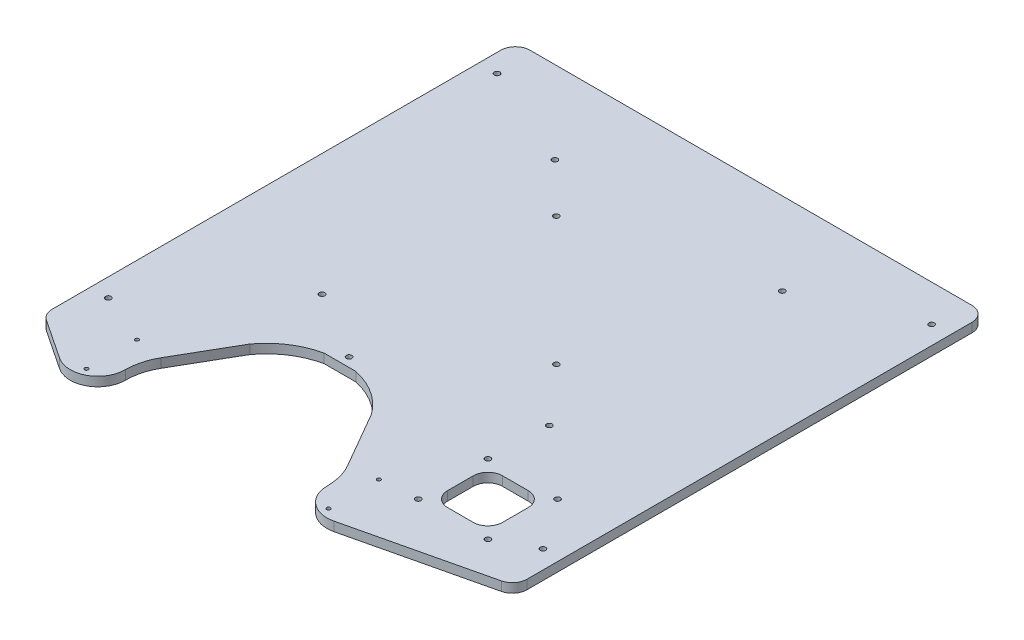
SolidWorks part; units mm, degrees
material "ABS PC"
ref_plane "Plan de face" through (0, 0, 0) normal (0, 0, 1) x (1, 0, 0)
ref_plane "Plan de dessus" through (0, 0, 0) normal (0, 1, 0) x (1, 0, 0)
ref_plane "Plan de droite" through (0, 0, 0) normal (1, 0, 0) x (0, 0, -1)
sketch "Esquisse1" plane through (0, 0, 0) normal (0, 1, 0) x (1, 0, 0)
  line L0 (-60.6815, -188.3301) -> (-75.8539, -214.6094) construction
  line L1 (-120.5, 31.2) -> (120.5, 31.2)
  line L2 (-128.5, 23.2) -> (-128.5, -221.5153)
  line L3 (-60.6815, -188.3301) -> (-75.8539, -214.6094)
  line L4 (128.5, 23.2) -> (128.5, -219.4674)
  line L5 (25.8539, -214.6094) -> (10.6815, -188.3301) construction
  line L6 (25.8539, -214.6094) -> (10.6815, -188.3301)
  line L7 (8.1815, -184) -> (10.6815, -188.3301)
  line L8 (-16.3766, -168) -> (-33.6234, -168) construction
  line L9 (-124.9334, -228.1745) -> (-103.3127, -242.5688)
  line L10 (122.3365, -227.2537) -> (48.4434, -244.6823)
  line L11 (-16.3766, -168) -> (-33.6234, -168)
  line L12 (-113.5, -220.8) -> (-123.5, -220.8) construction
  line L13 (-58.1815, -184) -> (-60.6815, -188.3301)
  line L15 (-123.5, -220.8) -> (-123.5, 31.2) construction
  line L16 (123.5, -220.8) -> (123.5, 31.2) construction
  line L18 (113.5, 31.2) -> (-113.5, 31.2) construction
  arc A0 (8.1815, -184) -> (-16.3766, -168) centre (-25, -208.0829) ccw construction
  arc A1 (8.1815, -184) -> (-16.3766, -168) centre (-25, -208.0829) ccw
  circle A2 centre (-91, -240.25) radius 1.95 construction
  arc A3 (-33.6234, -168) -> (-58.1815, -184) centre (-25, -208.0829) ccw construction
  arc A4 (30, -230.0829) -> (45, -245.0829) centre (45, -230.0829) ccw construction
  arc A5 (30, -230.0829) -> (25.8539, -214.6094) centre (-0.9469, -230.0829) ccw construction
  arc A6 (30, -230.0829) -> (25.8539, -214.6094) centre (-0.9469, -230.0829) ccw
  arc A7 (-95, -245.0829) -> (-80, -230.0829) centre (-95, -230.0829) ccw construction
  circle A8 centre (41, -212.75) radius 1
  circle A9 centre (41, -240.25) radius 1
  arc A10 (-120.5, 31.2) -> (-128.5, 23.2) centre (-120.5, 23.2) ccw
  arc A11 (120.5, 31.2) -> (128.5, 23.2) centre (120.5, 23.2) cw
  arc A12 (122.3365, -227.2537) -> (128.5, -219.4674) centre (120.5, -219.4674) ccw
  arc A13 (-128.5, -221.5153) -> (-124.9334, -228.1745) centre (-120.5, -221.5153) ccw
  arc A14 (-87.0138, -242.7801) -> (-80, -230.0829) centre (-95, -230.0829) ccw
  arc A15 (-75.8539, -214.6094) -> (-80, -230.0829) centre (-49.0531, -230.0829) ccw construction
  arc A16 (-75.8539, -214.6094) -> (-80, -230.0829) centre (-49.0531, -230.0829) ccw
  arc A17 (30, -230.0829) -> (42.3384, -244.8448) centre (45, -230.0829) ccw
  arc A18 (42.3384, -244.8448) -> (48.4434, -244.6823) centre (45, -230.0829) ccw
  arc A19 (-87.0138, -242.7801) -> (-103.3127, -242.5688) centre (-95, -230.0829) cw
  circle A20 centre (-91, -212.75) radius 1
  circle A21 centre (-91, -240.25) radius 1
  arc A22 (-33.6234, -168) -> (-58.1815, -184) centre (-25, -208.0829) ccw
  point P31 (-128.5, -225.8)
  point P44 (128.5, -225.8)
  dimension "D2" = 2
  dimension "D6" = 8
  dimension "D3" = 5
  dimension "D4" = 5
  dimension "D5" = 5
extrude "Boss.-Extru.1" add sketch "Esquisse1" against normal blind 5
sketch "Esquisse2" plane through (0, 0, 0) normal (0, 1, 0) x (1, 0, 0)
  circle A0 centre (-118.5, 11.2) radius 1.5
  circle A1 centre (-25, -163) radius 1.5
  circle A2 centre (118.5, 11.2) radius 1.5
  circle A3 centre (118.5, -200.8) radius 1.5
  circle A4 centre (-118.5, -200.8) radius 1.5
  dimension "D1" = 3
extrude "Enlèv. mat.-Extru.1" cut sketch "Esquisse2" against normal through all
sketch "Esquisse3" plane through (0, 0, 0) normal (0, 1, 0) x (1, 0, 0)
  circle A0 centre (62, -140.8) radius 1.5 construction
  circle A1 centre (62, -140.8) radius 1.5
  circle A2 centre (-62, -140.8) radius 1.5 construction
  circle A3 centre (-62, -140.8) radius 1.5
  circle A4 centre (62, -13.8) radius 1.5 construction
  circle A5 centre (62, -13.8) radius 1.5
  circle A6 centre (-62, -13.8) radius 1.5 construction
  circle A7 centre (-62, -13.8) radius 1.5
extrude "Enlèv. mat.-Extru.2" cut sketch "Esquisse3" against normal through all
sketch "Esquisse4" plane through (0, 0, 0) normal (0, 1, 0) x (1, 0, 0)
  circle A0 centre (-35, -40) radius 1.5 construction
  circle A1 centre (-35, -40) radius 1.5
  circle A2 centre (35, -110) radius 1.5 construction
  circle A3 centre (35, -110) radius 1.5
extrude "Enlèv. mat.-Extru.3" cut sketch "Esquisse4" against normal through all
sketch "Esquisse5" plane through (0, 0, 0) normal (0, 1, 0) x (1, 0, 0)
  line L0 (50.7314, -192.3) -> (108.7099, -192.3) construction
  line L1 (73, -177.3) -> (87, -177.3)
  line L2 (65, -185.3) -> (65, -199.3)
  line L3 (73, -207.3) -> (87, -207.3)
  line L4 (95, -185.3) -> (95, -199.3)
  line L5 (80, -150.3583) -> (80, -210.5946) construction
  circle A0 centre (61, -211.3) radius 1.5
  circle A1 centre (99, -211.3) radius 1.5
  circle A2 centre (99, -173.3) radius 1.5
  circle A3 centre (61, -173.3) radius 1.5
  arc A4 (65, -199.3) -> (73, -207.3) centre (73, -199.3) ccw
  arc A5 (87, -207.3) -> (95, -199.3) centre (87, -199.3) ccw
  arc A6 (87, -177.3) -> (95, -185.3) centre (87, -185.3) cw
  arc A7 (73, -177.3) -> (65, -185.3) centre (73, -185.3) ccw
  point P24 (95, -207.3)
  point P27 (95, -177.3)
  dimension "D1" = 3
  dimension "D3" = 8
  dimension "D2" = 30
extrude "Enlèv. mat.-Extru.5" cut sketch "Esquisse5" against normal through all
